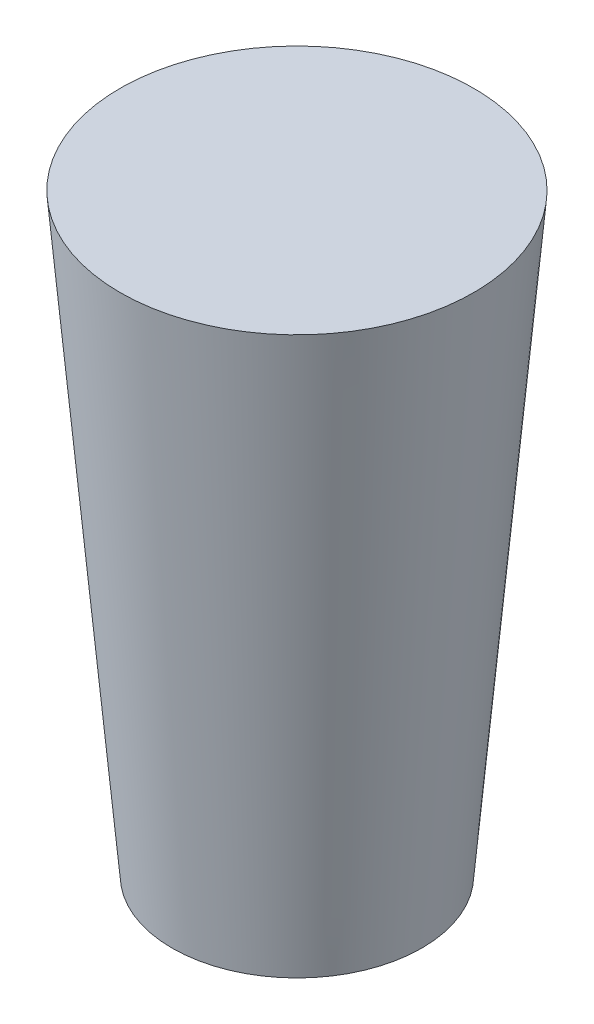
SolidWorks part; units mm, degrees
ref_plane "Front Plane" through (0, 0, 0) normal (0, 0, 1) x (1, 0, 0)
ref_plane "Top Plane" through (0, 0, 0) normal (0, 1, 0) x (1, 0, 0)
ref_plane "Right Plane" through (0, 0, 0) normal (1, 0, 0) x (0, 0, -1)
sketch "Sketch1" plane through (0, 0, 0) normal (0, 1, 0) x (1, 0, 0)
  circle A0 centre (0, 0) radius 10.522
extrude "Boss-Extrude1" add sketch "Sketch1" along normal blind 50 draft 5 draft outward yes
